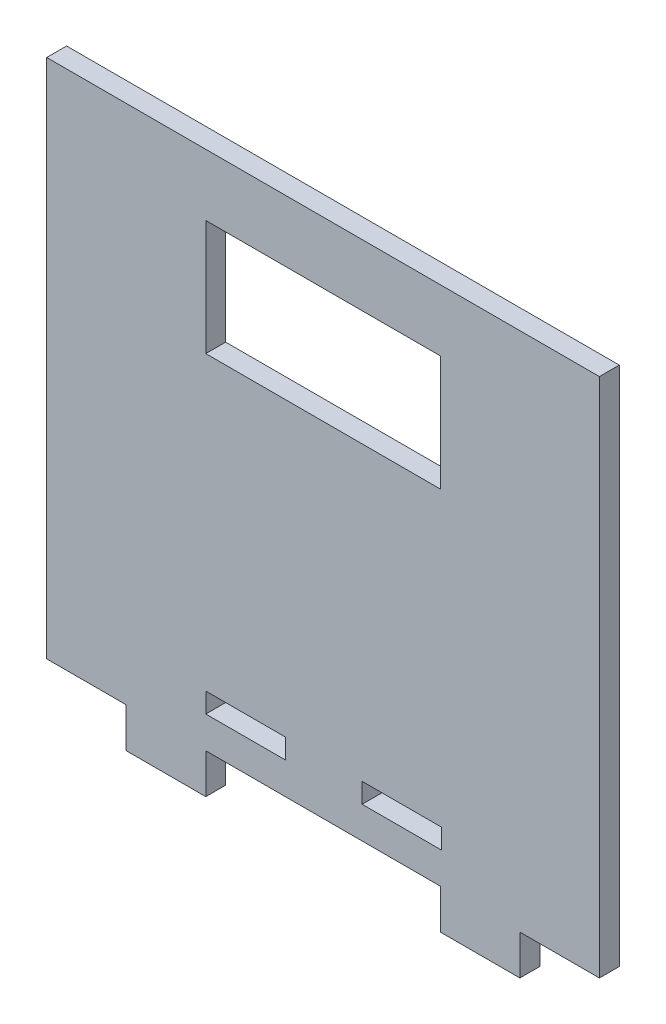
SolidWorks part; units mm, degrees
ref_plane "Front Plane" through (0, 0, 0) normal (0, 0, 1) x (1, 0, 0)
ref_plane "Top Plane" through (0, 0, 0) normal (0, 1, 0) x (1, 0, 0)
ref_plane "Right Plane" through (0, 0, 0) normal (1, 0, 0) x (0, 0, -1)
sketch "Sketch1" plane through (0, 0, 0) normal (0, 0, 1) x (1, 0, 0)
  line L0 (-57.9095, -57.5) -> (57.0545, -57.5) construction
  line L1 (-69.5, 65.5) -> (69.5, 65.5)
  line L2 (-69.5, 65.5) -> (-69.5, -65.5)
  line L3 (-69.5, -65.5) -> (69.5, -65.5)
  line L4 (69.5, 65.5) -> (69.5, -65.5)
  line L5 (-69.5, 65.5) -> (69.5, -65.5) construction
  line L6 (-69.5, -65.5) -> (69.5, 65.5) construction
  line L7 (-49.5, -65.5) -> (-29.5, -65.5)
  line L8 (-49.5, -65.5) -> (-49.5, -75.5)
  line L9 (-49.5, -75.5) -> (-29.5, -75.5)
  line L10 (-29.5, -65.5) -> (-29.5, -75.5)
  line L11 (29.5, -65.5) -> (49.5, -65.5)
  line L12 (29.5, -65.5) -> (29.5, -75.5)
  line L13 (29.5, -75.5) -> (49.5, -75.5)
  line L14 (49.5, -65.5) -> (49.5, -75.5)
  line L15 (-57.9095, -52.5) -> (57.0545, -52.5) construction
  line L16 (0, -52.5) -> (0, 35.5) construction
  line L17 (-29.5, -57.5) -> (-9.5, -57.5)
  line L18 (-29.5, -57.5) -> (-29.5, -52.5)
  line L19 (-29.5, -52.5) -> (-9.5, -52.5)
  line L20 (-9.5, -57.5) -> (-9.5, -52.5)
  line L21 (29.8195, -57.5) -> (9.8195, -57.5)
  line L22 (29.8195, -57.5) -> (29.8195, -52.5)
  line L23 (29.8195, -52.5) -> (9.8195, -52.5)
  line L24 (9.8195, -57.5) -> (9.8195, -52.5)
  line L26 (29.5, 50) -> (-29.5, 50)
  line L27 (29.5, 50) -> (29.5, 21)
  line L28 (29.5, 21) -> (-29.5, 21)
  line L29 (-29.5, 50) -> (-29.5, 21)
  line L30 (29.5, 50) -> (-29.5, 21) construction
  line L31 (29.5, 21) -> (-29.5, 50) construction
  point P0 (0, 0)
  dimension "D1" = 139
  dimension "D2" = 131
  dimension "D3" = 20
  dimension "D4" = 20
  dimension "D5" = 59
  dimension "D6" = 20
  dimension "D7" = 8
  dimension "D8" = 13
  dimension "D9" = 20
  dimension "D10" = 20
  dimension "D11" = 88
  dimension "D12" = 29
  dimension "D13" = 59
  dimension "D14" = 10
  dimension "D15" = 10
extrude "Boss-Extrude2" add sketch "Sketch1" along normal blind 5 contours L4 L1 L2 L3 L29 L26 L27 L28 L20 L17 L18 L19 L21 L24 L23 L22 | L14 L3 L12 L13 | L10 L3 L8 L9
